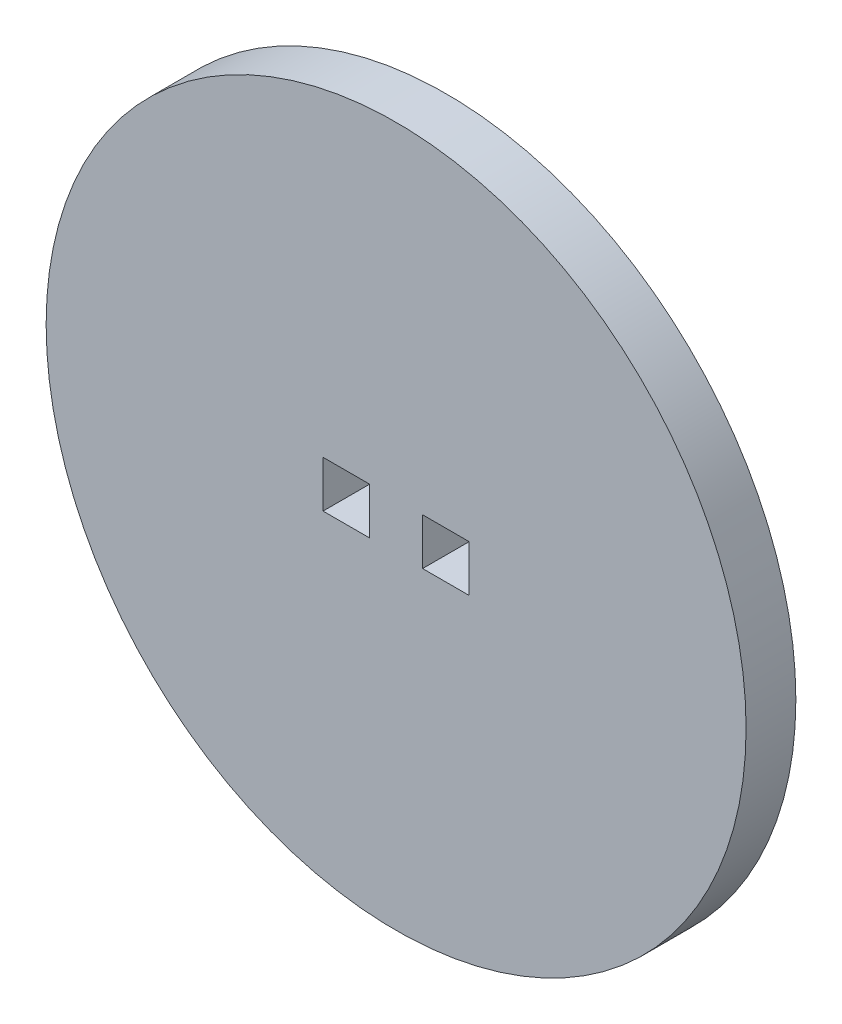
SolidWorks part; units mm, degrees
ref_plane "Front Plane" through (0, 0, 0) normal (0, 0, 1) x (1, 0, 0)
ref_plane "Top Plane" through (0, 0, 0) normal (0, 1, 0) x (1, 0, 0)
ref_plane "Right Plane" through (0, 0, 0) normal (1, 0, 0) x (0, 0, -1)
sketch "Sketch1" plane through (0, 0, 0) normal (0, 0, 1) x (1, 0, 0)
  line L0 (-1.5875, 0) -> (1.5875, 0) construction
  line L1 (1.5875, -1.5875) -> (4.7625, -1.5875) construction
  line L2 (1.5875, -1.5875) -> (1.5875, 1.5875) construction
  line L3 (1.5875, 1.5875) -> (4.7625, 1.5875) construction
  line L4 (4.7625, -1.5875) -> (4.7625, 1.5875) construction
  line L5 (-4.7625, 1.5875) -> (-1.5875, 1.5875) construction
  line L6 (-4.7625, 1.5875) -> (-4.7625, -1.5875) construction
  line L7 (-4.7625, -1.5875) -> (-1.5875, -1.5875) construction
  line L8 (-1.5875, 1.5875) -> (-1.5875, -1.5875) construction
  line L9 (-4.6609, 1.4859) -> (-4.6609, -1.4859)
  line L10 (-4.6609, -1.4859) -> (-1.6891, -1.4859)
  line L11 (-1.6891, 1.4859) -> (-1.6891, -1.4859)
  line L12 (-4.6609, 1.4859) -> (-1.6891, 1.4859)
  line L13 (1.6891, -1.4859) -> (1.6891, 1.4859)
  line L14 (1.6891, 1.4859) -> (4.6609, 1.4859)
  line L15 (4.6609, -1.4859) -> (4.6609, 1.4859)
  line L16 (1.6891, -1.4859) -> (4.6609, -1.4859)
  circle A0 centre (0, 0) radius 22.225 construction
  circle A1 centre (0, 0) radius 22.3266
  point P13 (0, 0)
  dimension "D1" = 44.45
  dimension "D2" = 3.175
  dimension "D3" = 3.175
  dimension "D4" = 0.1016
  dimension "D5" = 0.1016
extrude "Boss-Extrude1" add sketch "Sketch1" along normal blind 3.175
equation "\"1.25i\"=4.63913"
